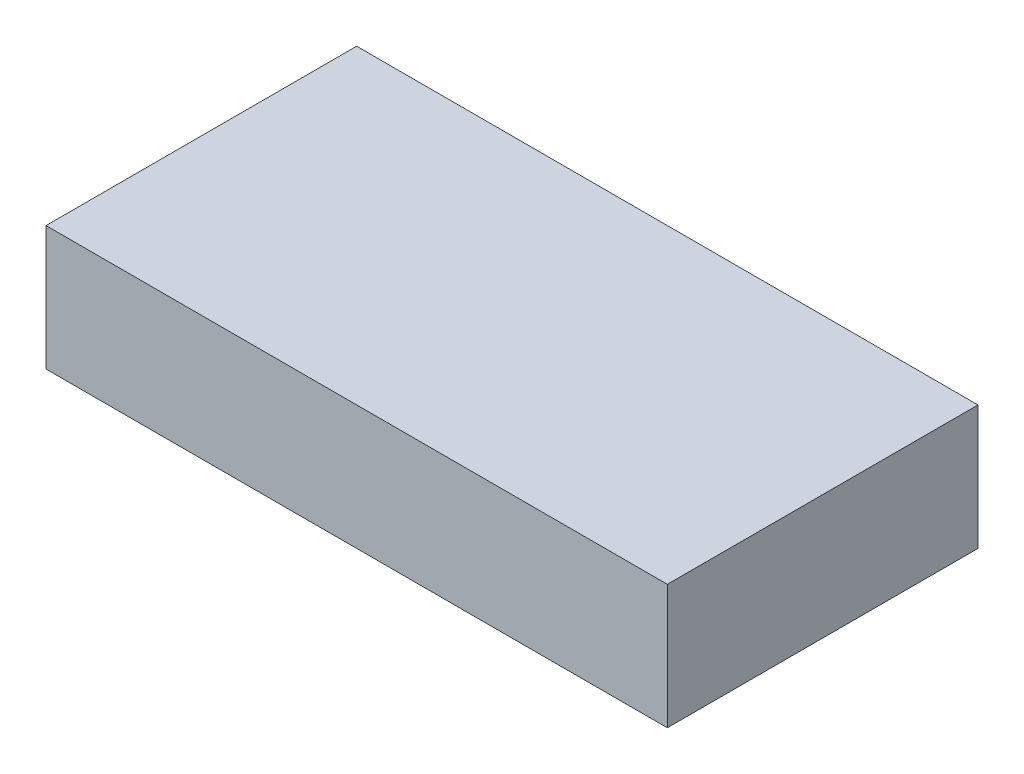
SolidWorks part; units mm, degrees
ref_plane "Front Plane" through (0, 0, 0) normal (0, 0, 1) x (1, 0, 0)
ref_plane "Top Plane" through (0, 0, 0) normal (0, 1, 0) x (1, 0, 0)
ref_plane "Right Plane" through (0, 0, 0) normal (1, 0, 0) x (0, 0, -1)
sketch "Sketch1" plane through (0, 0, 0) normal (0, 0, 1) x (1, 0, 0)
  line L0 (0, -2) -> (0, 2) construction
  line L1 (-10, 2) -> (10, 2)
  line L2 (-10, 2) -> (-10, -2)
  line L3 (-10, -2) -> (10, -2)
  line L4 (10, 2) -> (10, -2)
  line L5 (-10, 2) -> (10, -2) construction
  line L6 (-10, -2) -> (10, 2) construction
  line L7 (10, 0) -> (-10, 0) construction
  point P0 (0, 0)
  dimension "D1" = 4
  dimension "D2" = 20
extrude "Boss-Extrude1" add sketch "Sketch1" along normal blind 10 contours L1 L4 L3 L2
ref_plane "Plane1" through (0, -2, 0) normal (0, -1, 0) x (-1, 0, 0)
sketch "Sketch2" plane through (0, -2, 0) normal (0, -1, 0) x (-1, 0, 0)
  line L0 (0, 0) -> (0, -10) construction
  line L1 (10, 0) -> (-10, 0) construction
  line L2 (10, -10) -> (-10, -10) construction
  line L3 (-10, -5) -> (10, -5) construction
  line L4 (-10, -10) -> (-10, 0) construction
  line L5 (10, -10) -> (10, 0) construction
  circle A0 centre (0, -5) radius 4
  circle A1 centre (0, -5) radius 1.9
  circle A2 centre (0, -5) radius 1
  circle A3 centre (0, -5) radius 0.9
  circle A4 centre (0, -5) radius 0.4
  point P19 (0, -5)
  dimension "D1" = 8
  dimension "D2" = 3.8
  dimension "D3" = 2
  dimension "D4" = 1.8
  dimension "D5" = 0.8
extrude "Boss-Extrude2" add sketch "Sketch2" along normal blind 1 contours A0
ref_plane "Plane2" through (0, -3, 0) normal (0, -1, 0) x (-1, 0, 0)
sketch "Sketch5" plane through (0, -3, 0) normal (0, -1, 0) x (-1, 0, 0)
  line L0 (0, -9) -> (0, -1) construction
  line L1 (-2, -1.5359) -> (2, -1.5359) construction
  circle A0 centre (0, -5) radius 4 construction
  circle A1 centre (0, -5) radius 3.5
  dimension "D2" = 7
  dimension "D1" = 4
extrude "Cut-Extrude1" cut sketch "Sketch5" against normal blind 0.25 contours A1
sketch "Sketch6" plane through (0, -2, 0) normal (0, -1, 0) x (-1, 0, 0)
  line L0 (-10, -10) -> (-10, 0) construction
  line L1 (10, -10) -> (-10, -10) construction
  circle A0 centre (-7.25, -9.25) radius 0.25
  circle A1 centre (-8.25, -9.25) radius 0.25
  circle A2 centre (-9.25, -9.25) radius 0.25
  point P8 (0, 0)
  point P9 (0, 0)
  point P12 (-5.0935, -9.5329)
  point P13 (0, 0)
  point P14 (0, 0)
  dimension "D1" = 0.5
  dimension "D2" = 0.5
  dimension "D3" = 0.5
  dimension "D4" = 0.75
  dimension "D5" = 1
  dimension "D6" = 1
  dimension "D7" = 0.75
extrude "Boss-Extrude3" add sketch "Sketch6" along normal blind 0.25
